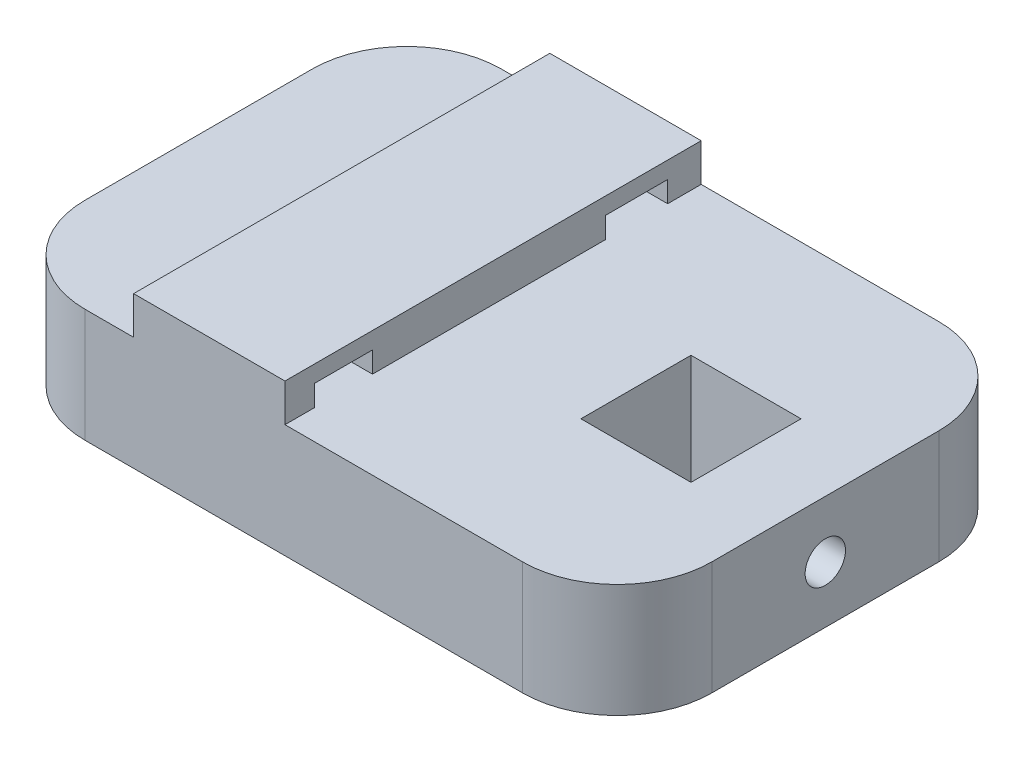
SolidWorks part; units mm, degrees
ref_plane "Front Plane" through (0, 0, 0) normal (0, 0, 1) x (1, 0, 0)
ref_plane "Top Plane" through (0, 0, 0) normal (0, 1, 0) x (1, 0, 0)
ref_plane "Right Plane" through (0, 0, 0) normal (1, 0, 0) x (0, 0, -1)
sketch "Sketch1" plane through (0, 0, 0) normal (0, 0, 1) x (1, 0, 0)
  line L0 (41.4001, 5) -> (28.9001, 5)
  line L1 (28.9001, -10) -> (41.4001, -10)
  line L2 (41.4001, -10) -> (41.4001, 5)
  line L3 (-28.9001, -10) -> (28.9001, -10)
  line L4 (28.9001, 5) -> (-2.4999, 5)
  line L5 (-2.4999, 5) -> (-2.4999, 10)
  line L6 (-2.4999, 10) -> (-22.4999, 10)
  line L7 (-22.4999, 10) -> (-22.4999, 5)
  line L8 (-22.4999, 5) -> (-28.9001, 5)
  line L9 (-28.9001, 5) -> (-41.4001, 5)
  line L10 (-41.4001, 5) -> (-41.4001, -10)
  line L11 (-41.4001, -10) -> (-28.9001, -10)
extrude "Boss-Extrude1" add sketch "Sketch1" along normal blind 55
sketch "Sketch2" plane through (0, 5, 0) normal (0, 1, 0) x (1, 0, 0)
  line L0 (41.4001, -27.5) -> (23.6516, -27.5)
  line L1 (41.4001, -55) -> (41.4001, 0) construction
  line L3 (30.9242, -20.2274) -> (16.379, -20.2274)
  line L4 (30.9242, -20.2274) -> (30.9242, -34.7726)
  line L5 (30.9242, -34.7726) -> (16.379, -34.7726)
  line L6 (16.379, -20.2274) -> (16.379, -34.7726)
  line L7 (30.9242, -20.2274) -> (16.379, -34.7726) construction
  line L8 (30.9242, -34.7726) -> (16.379, -20.2274) construction
extrude "Cut-Extrude1" cut sketch "Sketch2" against normal blind 55
sketch "Sketch3" plane through (-2.4999, 0, 0) normal (1, 0, 0) x (0, 0, -1)
  line L0 (-55, 5) -> (0, 5) construction
  line L1 (-51.1092, 7.7771) -> (-43.436, 7.7771)
  line L2 (-51.1092, 7.7771) -> (-51.1092, 5)
  line L3 (-51.1092, 5) -> (-43.436, 5)
  line L4 (-43.436, 7.7771) -> (-43.436, 5)
  line L6 (-12.6151, 7.7771) -> (-4.4303, 7.7771)
  line L7 (-12.6151, 7.7771) -> (-12.6151, 5)
  line L8 (-12.6151, 5) -> (-4.4303, 5)
  line L9 (-4.4303, 7.7771) -> (-4.4303, 5)
extrude "Cut-Extrude2" cut sketch "Sketch3" against normal blind 55
sketch "Sketch4" plane through (41.4001, 0, 0) normal (1, 0, 0) x (0, 0, -1)
  circle A0 centre (-27.5, -2.5164) radius 2.666
extrude "Cut-Extrude3" cut sketch "Sketch4" against normal blind 20
fillet "Fillet1" radius 12.5 4 edges at (-41.4001, -2.5, 0) (-41.4001, -2.5, 55) (41.4001, -2.5, 0) (41.4001, -2.5, 55)
